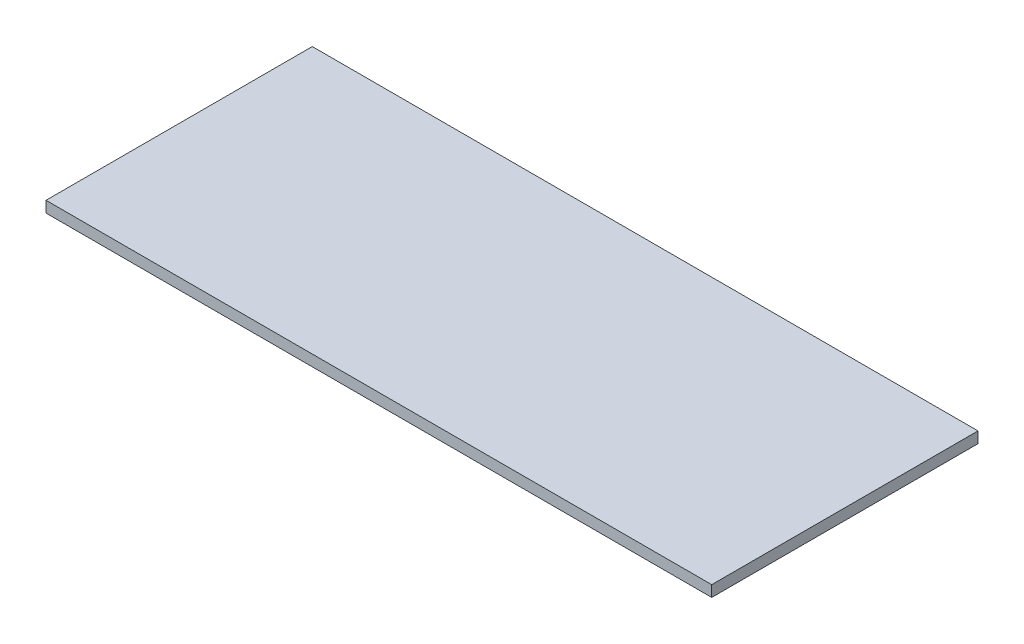
SolidWorks part; units mm, degrees
ref_plane "Front Plane" through (0, 0, 0) normal (0, 0, 1) x (1, 0, 0)
ref_plane "Top Plane" through (0, 0, 0) normal (0, 1, 0) x (1, 0, 0)
ref_plane "Right Plane" through (0, 0, 0) normal (1, 0, 0) x (0, 0, -1)
sketch "Sketch1" plane through (0, 0, 0) normal (0, 1, 0) x (1, 0, 0)
  line L1 (-19050, -7620) -> (19050, -7620)
  line L2 (-19050, -7620) -> (-19050, 7620)
  line L3 (-19050, 7620) -> (19050, 7620)
  line L4 (19050, -7620) -> (19050, 7620)
  line L5 (-19050, -7620) -> (19050, 7620) construction
  line L6 (-19050, 7620) -> (19050, -7620) construction
  point P0 (0, 0)
  dimension "D1" = 38100
  dimension "D2" = 15240
extrude "Boss-Extrude1" add sketch "Sketch1" along normal blind 635
